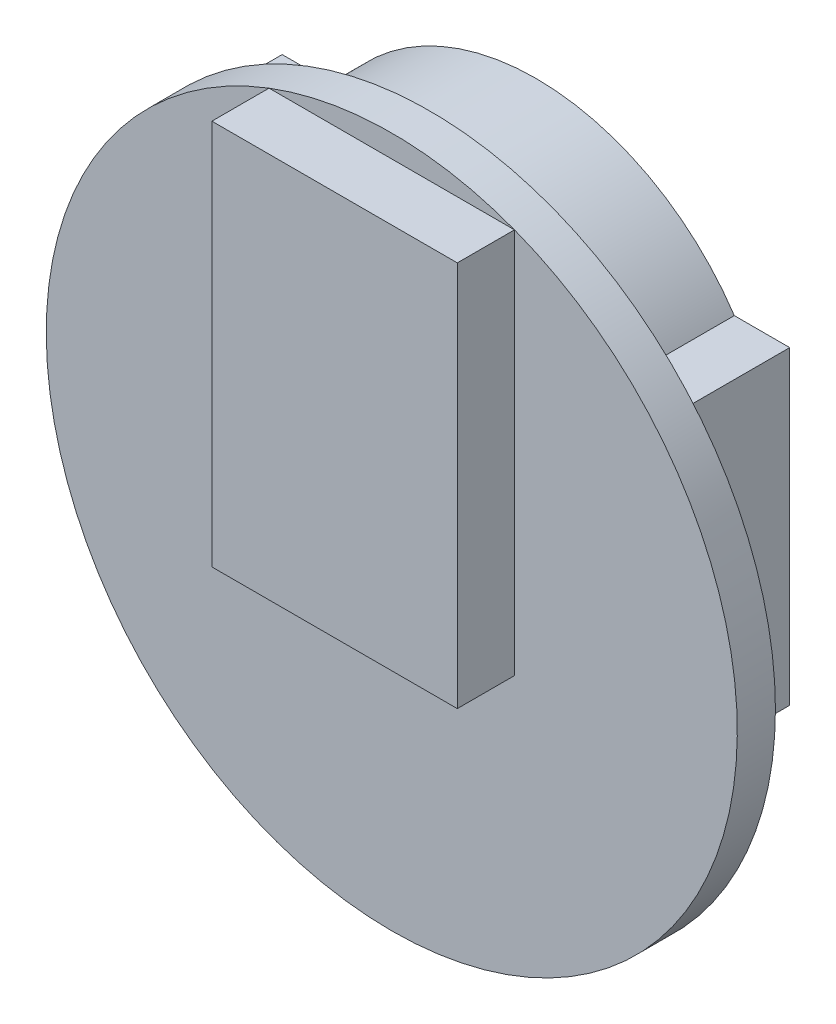
SolidWorks part; units mm, degrees
ref_plane "Plan de face" through (0, 0, 0) normal (0, 0, 1) x (1, 0, 0)
ref_plane "Plan de dessus" through (0, 0, 0) normal (0, 1, 0) x (1, 0, 0)
ref_plane "Plan de droite" through (0, 0, 0) normal (1, 0, 0) x (0, 0, -1)
sketch "Esquisse1" plane through (0, 0, 0) normal (0, 0, 1) x (1, 0, 0)
  circle A0 centre (-3.7082, 4.7631) radius 14.5
  dimension "D1" = 29
extrude "Boss.-Extru.1" add sketch "Esquisse1" along normal blind 1.6
sketch "Esquisse2" plane through (0, 0, 1.6) normal (0, 0, 1) x (1, 0, 0)
  line L0 (-3.7082, 19.2631) -> (-3.7082, -9.7369) construction
  line L1 (-8.8582, 18.3178) -> (1.4418, 18.3178)
  line L2 (-8.8582, 18.3178) -> (-8.8582, 2.1178)
  line L3 (-8.8582, 2.1178) -> (1.4418, 2.1178)
  line L4 (1.4418, 18.3178) -> (1.4418, 2.1178)
  circle A0 centre (-3.7082, 4.7631) radius 14.5 construction
  point P9 (-3.7082, 18.3178)
  dimension "D1" = 10.3
  dimension "D2" = 16.2
extrude "Boss.-Extru.2" add sketch "Esquisse2" along normal blind 2.4
sketch "Esquisse3" plane through (0, 0, 0) normal (0, 0, -1) x (-1, 0, 0)
  line L0 (7.7082, -4.2369) -> (14.3582, 0.7631)
  line L1 (-6.9418, 13.7631) -> (-4.6171, 13.7631)
  line L2 (-6.9418, 13.7631) -> (-6.9418, 0.7631)
  line L3 (-6.9418, 0.7631) -> (3.7082, 0.7631) construction
  line L4 (14.3582, 13.7631) -> (14.3582, 0.7631)
  line L5 (14.3582, 0.7631) -> (3.7082, 0.7631) construction
  line L7 (-0.2918, -4.2369) -> (7.7082, -4.2369)
  line L9 (-0.2918, -4.2369) -> (-6.9418, 0.7631)
  line L10 (3.7082, 19.2631) -> (3.7082, -9.7369) construction
  line L11 (12.0334, 13.7631) -> (14.3582, 13.7631)
  circle A1 centre (3.7082, 4.7631) radius 14.5 construction
  arc A2 (12.0334, 13.7631) -> (-4.6171, 13.7631) centre (3.7082, 8.2233) ccw
  point P11 (3.7082, -4.2369)
  dimension "D1" = 5
  dimension "D4" = 10
  dimension "D2" = 21.3
  dimension "D3" = 8
  dimension "D5" = 5.5
  dimension "D6" = 18
extrude "Boss.-Extru.3" add sketch "Esquisse3" along normal blind 4.45
sketch "Esquisse4" plane through (0, 0, 0) normal (0, 0, -1) x (-1, 0, 0)
  line L0 (3.7082, 19.2631) -> (3.7082, -9.7369) construction
  line L1 (0.7082, -4.2369) -> (6.7082, -4.2369)
  line L2 (0.7082, -4.2369) -> (0.7082, -8.2369)
  line L3 (0.7082, -8.2369) -> (6.7082, -8.2369)
  line L4 (6.7082, -4.2369) -> (6.7082, -8.2369)
  circle A0 centre (3.7082, 4.7631) radius 14.5 construction
  point P9 (3.7082, -4.2369)
  dimension "D1" = 6
  dimension "D2" = 4
  dimension "D3" = 5.5
extrude "Boss.-Extru.4" add sketch "Esquisse4" along normal blind 5.2
sketch "Esquisse5" plane through (0, 0, -5.2) normal (0, 0, -1) x (-1, 0, 0)
  line L0 (3.7082, -4.2369) -> (3.7082, -8.2369) construction
  line L1 (2.2082, -5.5869) -> (5.2082, -5.5869)
  line L2 (2.2082, -5.5869) -> (2.2082, -6.8869)
  line L3 (2.2082, -6.8869) -> (5.2082, -6.8869)
  line L4 (5.2082, -5.5869) -> (5.2082, -6.8869)
  line L5 (6.7082, -4.2369) -> (0.7082, -4.2369) construction
  line L6 (0.7082, -8.2369) -> (6.7082, -8.2369) construction
  line L7 (0.7082, -6.2369) -> (6.7082, -6.2369) construction
  line L8 (0.7082, -4.2369) -> (0.7082, -8.2369) construction
  line L9 (6.7082, -8.2369) -> (6.7082, -4.2369) construction
  point P16 (3.7082, -5.5869)
  point P17 (2.2082, -6.2369)
  dimension "D1" = 3
  dimension "D2" = 1.3
extrude "Boss.-Extru.5" add sketch "Esquisse5" along normal blind 1.6
sketch "Esquisse6" plane through (0, 0, 1.6) normal (0, 0, 1) x (1, 0, 0)
  line L0 (-3.7082, -9.7369) -> (-3.7082, 19.2631) construction
  line L1 (-18.2082, 4.7631) -> (10.7918, 4.7631) construction
  arc A0 (-8.8582, 18.3178) -> (1.4418, 18.3178) centre (-3.7082, 4.7631) ccw construction
  arc A1 (1.4418, 18.3178) -> (-8.8582, 18.3178) centre (-3.7082, 4.7631) ccw construction
  point P11 (-3.7082, 4.7631)
